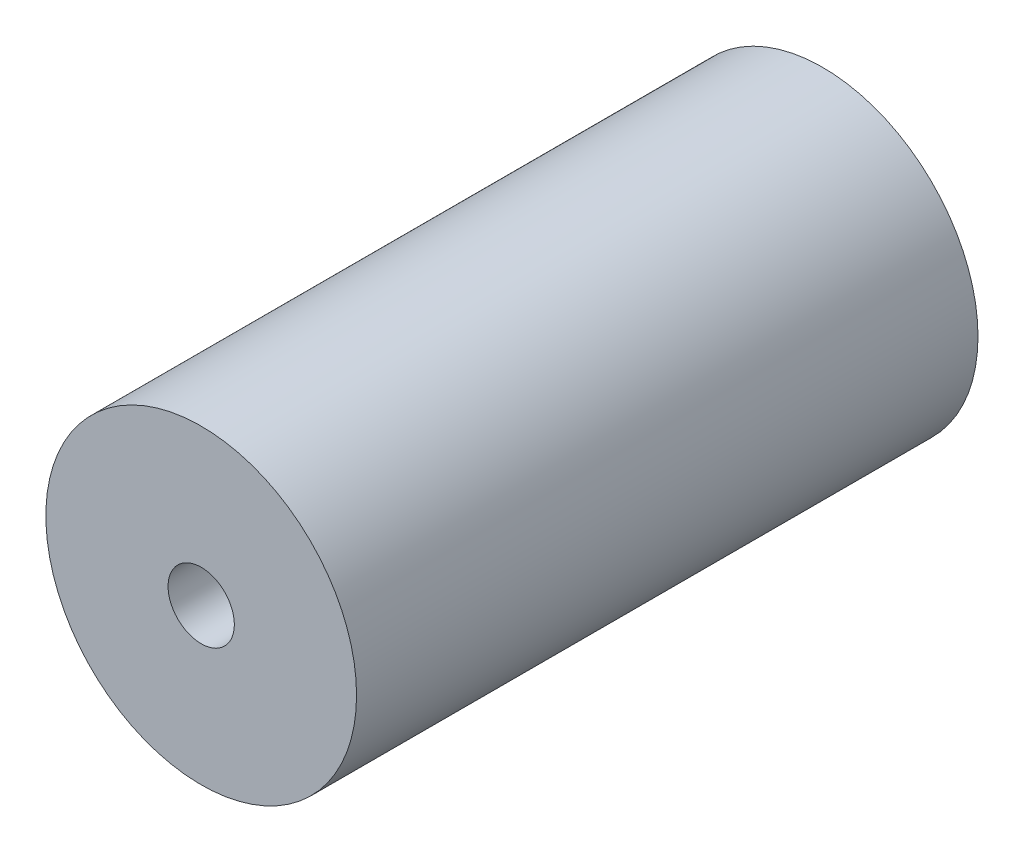
SolidWorks part; units mm, degrees
material "ｱｸﾘﾙ (中-上級の耐衝撃性)"
ref_plane "正面" through (0, 0, 0) normal (0, 0, 1) x (1, 0, 0)
ref_plane "平面" through (0, 0, 0) normal (0, 1, 0) x (1, 0, 0)
ref_plane "右側面" through (0, 0, 0) normal (1, 0, 0) x (0, 0, -1)
sketch "ｽｹｯﾁ1" plane through (0, 0, 0) normal (0, 0, 1) x (1, 0, 0)
  circle A0 centre (0, 0) radius 7.5
  dimension "D1" = 15
extrude "ﾎﾞｽ - 押し出し1" add sketch "ｽｹｯﾁ1" along normal blind 30
sketch "ｽｹｯﾁ2" plane through (0, 0, 30) normal (0, 0, 1) x (1, 0, 0)
  circle A0 centre (0, 0) radius 1.6
extrude "ｶｯﾄ - 押し出し1" cut sketch "ｽｹｯﾁ2" against normal through all
